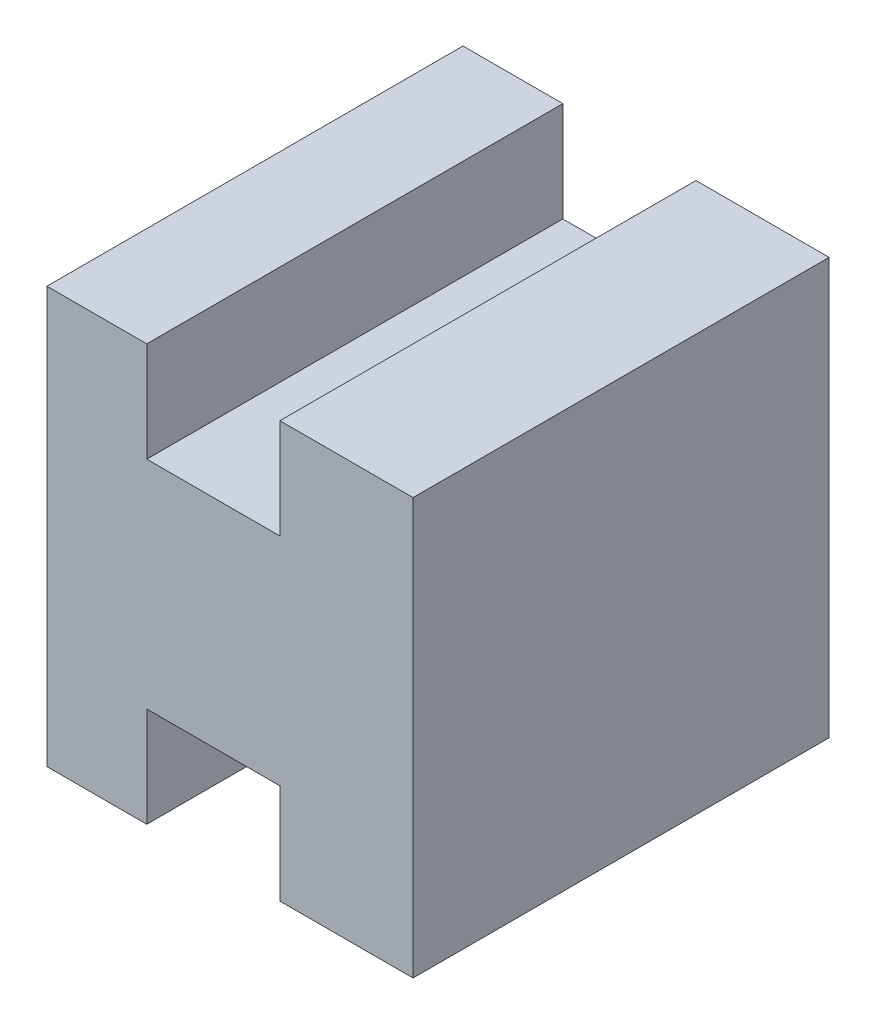
SolidWorks part; units mm, degrees
ref_plane "Front Plane" through (0, 0, 0) normal (0, 0, 1) x (1, 0, 0)
ref_plane "Top Plane" through (0, 0, 0) normal (0, 1, 0) x (1, 0, 0)
ref_plane "Right Plane" through (0, 0, 0) normal (1, 0, 0) x (0, 0, -1)
sketch "Sketch1" plane through (0, 0, 0) normal (0, 0, 1) x (1, 0, 0)
  line L0 (-90.6146, 45.4594) -> (-87.6146, 45.4594)
  line L1 (-87.6146, 45.4594) -> (-87.6146, 42.4594)
  line L2 (-90.6146, 45.4594) -> (-90.6146, 32.9594)
  line L3 (-90.6146, 32.9594) -> (-87.6146, 32.9594)
  line L4 (-87.6146, 32.9594) -> (-87.6146, 35.9594)
  line L5 (-87.6146, 35.9594) -> (-83.6146, 35.9594)
  line L6 (-83.6146, 35.9594) -> (-83.6146, 32.9594)
  line L7 (-83.6146, 32.9594) -> (-79.6146, 32.9594)
  line L8 (-87.6146, 42.4594) -> (-83.6146, 42.4594)
  line L9 (-83.6146, 42.4594) -> (-83.6146, 45.4594)
  line L10 (-83.6146, 45.4594) -> (-79.6146, 45.4594)
  line L12 (-79.6146, 45.4594) -> (-79.6146, 32.9594)
extrude "Boss-Extrude2" add sketch "Sketch1" along normal blind 12.5
